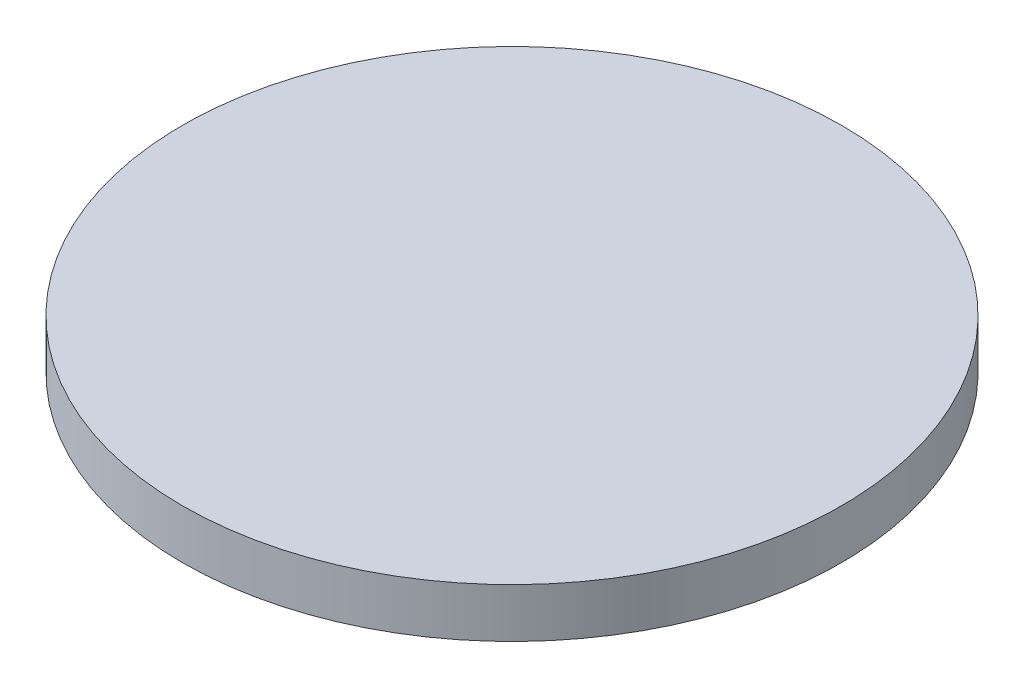
SolidWorks part; units mm, degrees
material "Plain Carbon Steel"
ref_plane "Front Plane" through (0, 0, 0) normal (0, 0, 1) x (1, 0, 0)
ref_plane "Top Plane" through (0, 0, 0) normal (0, 1, 0) x (1, 0, 0)
ref_plane "Right Plane" through (0, 0, 0) normal (1, 0, 0) x (0, 0, -1)
sketch "Sketch1" plane through (0, 0, 0) normal (0, 1, 0) x (1, 0, 0)
  circle A0 centre (0, 0) radius 20.32
  dimension "D1" = 40.64
extrude "Boss-Extrude1" add sketch "Sketch1" along normal blind 3.0378
